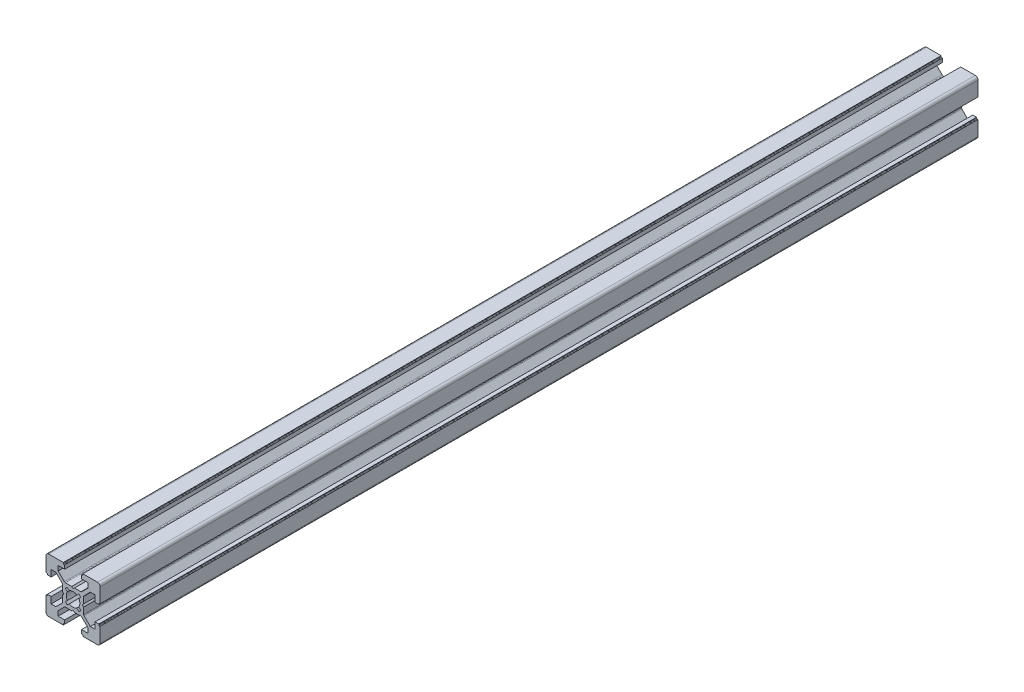
SolidWorks part; units mm, degrees
ref_plane "Спереди" through (0, 0, 0) normal (0, 0, 1) x (1, 0, 0)
ref_plane "Сверху" through (0, 0, 0) normal (0, 1, 0) x (1, 0, 0)
ref_plane "Справа" through (0, 0, 0) normal (1, 0, 0) x (0, 0, -1)
sketch "Sketch1" plane through (0, 0, 0) normal (0, 0, 1) x (1, 0, 0)
  line L0 (0, 10) -> (0, -10) construction
  line L1 (-10, -10) -> (10, -10) construction
  line L2 (-10, -10) -> (-10, 10) construction
  line L3 (-10, 10) -> (10, 10) construction
  line L4 (10, -10) -> (10, 10) construction
  line L5 (-10, -10) -> (10, 10) construction
  line L6 (-10, 10) -> (10, -10) construction
  line L7 (-10, 0) -> (10, 0) construction
  line L8 (0, 3.9) -> (-2.8444, 3.9)
  line L9 (-3.1979, 4.0464) -> (-5.5, 6.3485)
  line L10 (-5.5, 6.3485) -> (-5.5, 8.1)
  line L11 (-5.5, 8.1) -> (-3.1, 8.1)
  line L12 (-3.1, 8.1) -> (-3.1, 9.5)
  line L13 (-3.1, 9.5) -> (-3.4, 9.5)
  line L14 (-3.6, 9.7) -> (-3.6, 10)
  line L15 (-3.6, 10) -> (-9, 10)
  line L16 (-10, 3.6) -> (-10, 9)
  line L17 (-9.7, 3.6) -> (-10, 3.6)
  line L18 (-9.5, 3.1) -> (-9.5, 3.4)
  line L19 (-8.1, 3.1) -> (-9.5, 3.1)
  line L20 (-8.1, 5.5) -> (-8.1, 3.1)
  line L21 (-6.3485, 5.5) -> (-8.1, 5.5)
  line L22 (-4.0464, 3.1979) -> (-6.3485, 5.5)
  line L23 (-3.9, 0) -> (-3.9, 2.8444)
  line L24 (3.9, 0) -> (3.9, 2.8444)
  line L25 (4.0464, 3.1979) -> (6.3485, 5.5)
  line L26 (6.3485, 5.5) -> (8.1, 5.5)
  line L27 (8.1, 5.5) -> (8.1, 3.1)
  line L28 (8.1, 3.1) -> (9.5, 3.1)
  line L29 (9.5, 3.1) -> (9.5, 3.4)
  line L30 (9.7, 3.6) -> (10, 3.6)
  line L31 (10, 3.6) -> (10, 9)
  line L32 (3.6, 10) -> (9, 10)
  line L33 (3.6, 9.7) -> (3.6, 10)
  line L34 (3.1, 9.5) -> (3.4, 9.5)
  line L35 (3.1, 8.1) -> (3.1, 9.5)
  line L36 (5.5, 8.1) -> (3.1, 8.1)
  line L37 (5.5, 6.3485) -> (5.5, 8.1)
  line L38 (3.1979, 4.0464) -> (5.5, 6.3485)
  line L39 (0, 3.9) -> (2.8444, 3.9)
  line L40 (0, -3.9) -> (2.8444, -3.9)
  line L41 (3.1979, -4.0464) -> (5.5, -6.3485)
  line L42 (5.5, -6.3485) -> (5.5, -8.1)
  line L43 (5.5, -8.1) -> (3.1, -8.1)
  line L44 (3.1, -8.1) -> (3.1, -9.5)
  line L45 (3.1, -9.5) -> (3.4, -9.5)
  line L46 (3.6, -9.7) -> (3.6, -10)
  line L47 (3.6, -10) -> (9, -10)
  line L48 (10, -3.6) -> (10, -9)
  line L49 (9.7, -3.6) -> (10, -3.6)
  line L50 (9.5, -3.1) -> (9.5, -3.4)
  line L51 (8.1, -3.1) -> (9.5, -3.1)
  line L52 (8.1, -5.5) -> (8.1, -3.1)
  line L53 (6.3485, -5.5) -> (8.1, -5.5)
  line L54 (4.0464, -3.1979) -> (6.3485, -5.5)
  line L55 (3.9, 0) -> (3.9, -2.8444)
  line L56 (-3.9, 0) -> (-3.9, -2.8444)
  line L57 (-4.0464, -3.1979) -> (-6.3485, -5.5)
  line L58 (-6.3485, -5.5) -> (-8.1, -5.5)
  line L59 (-8.1, -5.5) -> (-8.1, -3.1)
  line L60 (-8.1, -3.1) -> (-9.5, -3.1)
  line L61 (-9.5, -3.1) -> (-9.5, -3.4)
  line L62 (-9.7, -3.6) -> (-10, -3.6)
  line L63 (-10, -3.6) -> (-10, -9)
  line L64 (-3.6, -10) -> (-9, -10)
  line L65 (-3.6, -9.7) -> (-3.6, -10)
  line L66 (-3.1, -9.5) -> (-3.4, -9.5)
  line L67 (-3.1, -8.1) -> (-3.1, -9.5)
  line L68 (-5.5, -8.1) -> (-3.1, -8.1)
  line L69 (-5.5, -6.3485) -> (-5.5, -8.1)
  line L70 (-3.1979, -4.0464) -> (-5.5, -6.3485)
  line L71 (0, -3.9) -> (-2.8444, -3.9)
  line L72 (2.0856, -1.3785) -> (2.8284, -2.1213)
  line L73 (2.0856, 1.3785) -> (2.8284, 2.1213)
  line L74 (2.8284, 2.1213) -> (2.1213, 2.8284)
  line L75 (2.1213, -2.8284) -> (2.8284, -2.1213)
  line L76 (1.3785, -2.0856) -> (2.1213, -2.8284)
  line L77 (1.3785, 2.0856) -> (2.1213, 2.8284)
  line L78 (-1.3785, -2.0856) -> (-2.1213, -2.8284)
  line L79 (-2.8284, -2.1213) -> (-2.1213, -2.8284)
  line L80 (-2.0856, -1.3785) -> (-2.8284, -2.1213)
  line L81 (-2.0856, 1.3785) -> (-2.8284, 2.1213)
  line L82 (-2.1213, 2.8284) -> (-2.8284, 2.1213)
  line L83 (-1.3785, 2.0856) -> (-2.1213, 2.8284)
  line L84 (-0.5, 3.9) -> (0, 3.4)
  line L85 (0, 3.4) -> (0.5, 3.9)
  line L86 (3.9, 0.5) -> (3.4, 0)
  line L87 (3.4, 0) -> (3.9, -0.5)
  line L88 (0.5, -3.9) -> (0, -3.4)
  line L89 (0, -3.4) -> (-0.5, -3.9)
  line L90 (-3.9, -0.5) -> (-3.4, 0)
  line L91 (-3.4, 0) -> (-3.9, 0.5)
  circle A0 centre (0, 0) radius 2.5
  arc A1 (-9, 10) -> (-10, 9) centre (-9, 9) ccw
  arc A2 (-2.8444, 3.9) -> (-3.1979, 4.0464) centre (-2.8444, 4.4) cw
  arc A3 (-3.4, 9.5) -> (-3.6, 9.7) centre (-3.4, 9.7) cw
  arc A4 (-9.5, 3.4) -> (-9.7, 3.6) centre (-9.7, 3.4) ccw
  arc A5 (-3.9, 2.8444) -> (-4.0464, 3.1979) centre (-4.4, 2.8444) ccw
  arc A6 (10, 9) -> (9, 10) centre (9, 9) ccw
  arc A7 (3.9, 2.8444) -> (4.0464, 3.1979) centre (4.4, 2.8444) cw
  arc A8 (9.5, 3.4) -> (9.7, 3.6) centre (9.7, 3.4) cw
  arc A9 (3.4, 9.5) -> (3.6, 9.7) centre (3.4, 9.7) ccw
  arc A10 (2.8444, 3.9) -> (3.1979, 4.0464) centre (2.8444, 4.4) ccw
  arc A11 (9, -10) -> (10, -9) centre (9, -9) ccw
  arc A12 (2.8444, -3.9) -> (3.1979, -4.0464) centre (2.8444, -4.4) cw
  arc A13 (3.4, -9.5) -> (3.6, -9.7) centre (3.4, -9.7) cw
  arc A14 (9.5, -3.4) -> (9.7, -3.6) centre (9.7, -3.4) ccw
  arc A15 (3.9, -2.8444) -> (4.0464, -3.1979) centre (4.4, -2.8444) ccw
  arc A16 (-10, -9) -> (-9, -10) centre (-9, -9) ccw
  arc A17 (-3.9, -2.8444) -> (-4.0464, -3.1979) centre (-4.4, -2.8444) cw
  arc A18 (-9.5, -3.4) -> (-9.7, -3.6) centre (-9.7, -3.4) cw
  arc A19 (-3.4, -9.5) -> (-3.6, -9.7) centre (-3.4, -9.7) ccw
  arc A20 (-2.8444, -3.9) -> (-3.1979, -4.0464) centre (-2.8444, -4.4) ccw
  point P0 (0, 0)
  point P42 (0, 0)
  point P70 (0, 0)
  point P98 (0, 0)
  point P126 (0, 0)
  point P139 (0, 0)
  point P152 (0, 0)
  dimension "D3" = 5
  dimension "D4" = 2
  dimension "D12" = 0.5
  dimension "D13" = 0.2
  dimension "D15" = 1
  dimension "D1" = 20
  dimension "D2" = 20
  dimension "D5" = 6.2
  dimension "D6" = 7.2
  dimension "D7" = 1.9
  dimension "D8" = 0.5
  dimension "D10" = 1.2
  dimension "D11" = 6.1
  dimension "D16" = 3.5
  dimension "D18" = 0.5
  dimension "D14" = 4
  dimension "D17" = 4
  dimension "D19" = 4
extrude "Extrude1" add sketch "Sketch1" along normal blind 324 contours A20 L71 L89 L88 L40 A12 L41 L42 L43 L44 L45 A13 L46 L47 A11 L48 L49 A14 L50 L51 L52 L53 L54 A15 L55 L87 L86 L24 A7 L25 L26 L27 L28 L29 A8 L30 L31 A6 L32 L33 A9 L34 L35 L36 L37 L38 A10 L39 L85 L84 L8
